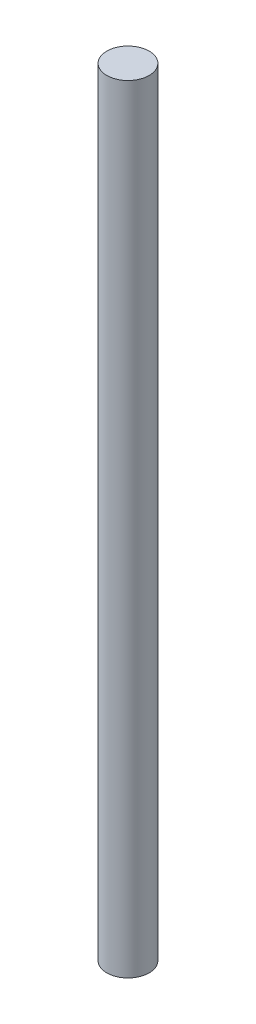
SolidWorks part; units mm, degrees
ref_plane "Plano frontal" through (0, 0, 0) normal (0, 0, 1) x (1, 0, 0)
ref_plane "Plano superior" through (0, 0, 0) normal (0, 1, 0) x (1, 0, 0)
ref_plane "Plano direito" through (0, 0, 0) normal (1, 0, 0) x (0, 0, -1)
sketch "Esboço1" plane through (0, 0, 0) normal (0, 1, 0) x (1, 0, 0)
  circle A0 centre (0, 0) radius 9.525
  dimension "D1" = 19.05
extrude "Ressalto-extrusão1" add sketch "Esboço1" along normal blind 350
